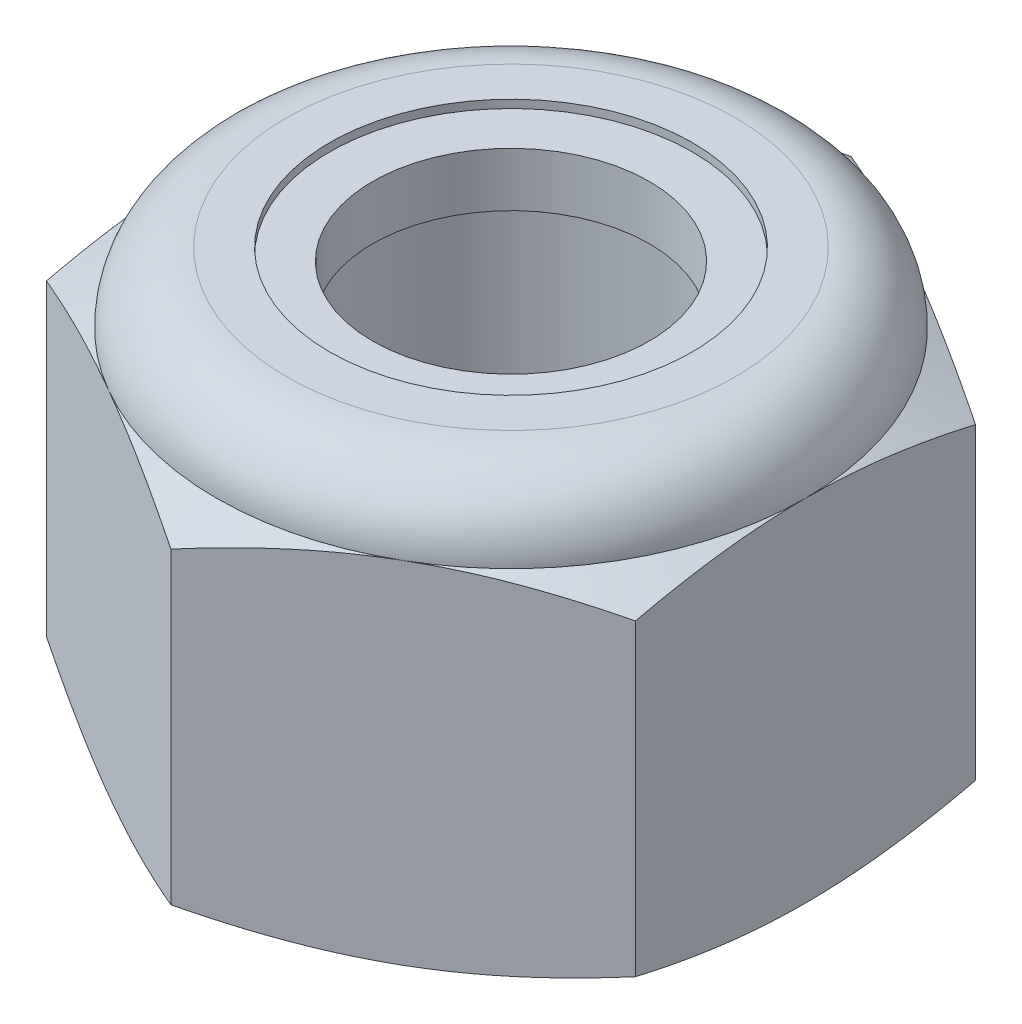
SolidWorks part; units mm, degrees
ref_plane "Front" through (0, 0, 0) normal (0, 0, 1) x (1, 0, 0)
ref_plane "Top" through (0, 0, 0) normal (0, 1, 0) x (1, 0, 0)
ref_plane "Right" through (0, 0, 0) normal (1, 0, 0) x (0, 0, -1)
sketch "Sketch1" plane through (0, 0, 0) normal (0, 1, 0) x (1, 0, 0)
  line L1 (0, 6.4158) -> (-5.5563, 3.2079)
  line L2 (-5.5563, 3.2079) -> (-5.5563, -3.2079)
  line L3 (-5.5563, -3.2079) -> (0, -6.4158)
  line L4 (0, -6.4158) -> (5.5562, -3.2079)
  line L5 (5.5562, -3.2079) -> (5.5562, 3.2079)
  line L6 (5.5562, 3.2079) -> (0, 6.4158)
  circle A0 centre (0, 0) radius 5.5563 construction
  dimension "Hex Flats" = 11.1125
extrude "Extrude1" add sketch "Sketch1" along normal blind 7.9375
sketch "Sketch2" plane through (0, 0, 0) normal (1, 0, 0) x (0, 0, -1)
  line L0 (-3.175, 0) -> (-3.175, 7.9375) construction
  line L1 (0, 0) -> (3.175, 0)
  line L2 (0, 0) -> (0, 7.9375)
  line L3 (0, 7.9375) -> (3.175, 7.9375)
  line L4 (3.175, 0) -> (3.175, 7.9375)
  line L5 (-3.2079, 7.9375) -> (3.2079, 7.9375) construction
  line L7 (0, -3.175) -> (0, 0) construction
  dimension "Thread Dia" = 6.35
revolve "Revolve1" add sketch "Sketch2" angle 360 about L7
sketch "Sketch3" plane through (0, 0, 0) normal (1, 0, 0) x (0, 0, -1)
  line L0 (3.175, 7.9375) -> (-3.175, 7.9375) construction
  line L1 (-3.175, 7.9375) -> (-3.175, 6.6675) construction
  line L2 (-3.175, 6.6675) -> (3.175, 7.9375) construction
  line L3 (3.175, 7.9375) -> (3.2061, 7.7818) construction
  line L4 (3.2061, 7.7818) -> (3.4241, 6.6922)
  line L5 (3.4241, 6.6922) -> (2.6722, 6.9465)
  line L6 (2.6722, 6.9465) -> (2.6099, 7.2579)
  line L7 (2.6099, 7.2579) -> (3.2061, 7.7818)
  line L8 (2.641, 7.1022) -> (3.3151, 7.237) construction
  line L9 (3.175, 7.9375) -> (3.175, 7.209) construction
  line L10 (3.175, 7.209) -> (-3.175, 5.939) construction
  line L11 (-3.175, 5.939) -> (-3.175, 6.6675) construction
  line L12 (-0.2727, 7.9375) -> (0.2727, 5.2105) construction
  line L13 (-3.175, 0) -> (-3.175, 7.9375) construction
  line L14 (0, 7.9375) -> (3.175, 7.9375) construction
  line L15 (3.175, 0) -> (3.175, 7.9375) construction
  point P13 (0, 6.574)
  dimension "D1" = 0.1588
  dimension "D2" = 0.3175
  dimension "Thread Pitch" = 1.27
  dimension "D4" = 60
  dimension "D5" = 1.27
revolve "Cut-Revolve1" [suppressed] cut sketch "Sketch3" angle 360 about L12
pattern_linear "LPattern1" [suppressed] count 6 spacing 1.27 along (0, 1, 0) count 2 spacing 1.27 along (0, 1, 0)
sketch "Sketch4" plane through (0, 0, 0) normal (1, 0, 0) x (0, 0, -1)
  line L0 (0, 7.9375) -> (3.175, 7.9375)
  line L1 (3.175, 7.9375) -> (2.6099, 7.674)
  line L2 (2.6099, 7.674) -> (2.6099, 0.2635)
  line L3 (2.6099, 0.2635) -> (3.175, 0)
  line L4 (3.175, 0) -> (0, 0)
  line L5 (0, 0) -> (0, 7.9375)
  line L6 (3.175, 0) -> (3.175, 7.9375) construction
  line L7 (0, 7.9375) -> (3.175, 7.9375) construction
  line L8 (0, 0) -> (3.175, 0) construction
  line L9 (0, 0) -> (0, 7.9375) construction
  line L10 (0, 7.9375) -> (0, 8.561) construction
  dimension "D1" = 25
revolve "Cut-Revolve2" [suppressed] cut sketch "Sketch4" angle 360 about L10
combine bodies "Combine1" operation type subtract main body 108 bodies to subtract 109
sketch "Sketch5" plane through (0, 0, 0) normal (1, 0, 0) x (0, 0, -1)
  line L0 (0, 0) -> (5.5563, 0)
  line L1 (5.5563, 0) -> (6.4158, 0.4008)
  line L2 (6.4158, 0.4008) -> (6.4158, 6.2138)
  line L3 (6.4158, 6.2138) -> (5.5563, 6.6146)
  line L4 (4.2333, 7.9375) -> (4.2333, 9.2075)
  line L5 (4.2333, 9.2075) -> (7.6858, 9.2075)
  line L6 (7.6858, 9.2075) -> (7.6858, -1.27)
  line L7 (7.6858, -1.27) -> (0, -1.27)
  line L8 (0, -1.27) -> (0, 0)
  line L9 (5.5563, 6.6146) -> (5.5563, 0) construction
  line L10 (0, 0) -> (3.175, 0) construction
  line L13 (6.4158, 3.3073) -> (7.6858, 3.3073) construction
  line L14 (6.4158, 7.9375) -> (6.4158, 0) construction
  line L15 (0, 0) -> (0, 9.2075) construction
  line L20 (0, 9.2075) -> (4.2333, 9.2075) construction
  line L22 (0, 7.9375) -> (3.175, 7.9375) construction
  arc A0 (5.5563, 6.6146) -> (4.2333, 7.9375) centre (4.2333, 6.6146) ccw
  dimension "D1" = 25
  dimension "D2" = 1.27
  dimension "D3" = 7.9375
  dimension "D4" = 1.3229
revolve "Cut-Revolve3" cut sketch "Sketch5" angle 360 about L15
sketch "Sketch6" plane through (0, 0, 0) normal (1, 0, 0) x (0, 0, -1)
  line L0 (0, 6.6146) -> (5.4039, 6.6146)
  line L1 (4.2333, 7.7851) -> (3.4216, 7.7851)
  line L2 (0, 9.2075) -> (0, 6.6146)
  line L3 (3.4216, 9.2075) -> (0, 9.2075)
  line L4 (0, 9.2075) -> (4.2333, 9.2075) construction
  line L5 (0, 0) -> (0, 9.2075) construction
  line L6 (0, 9.2075) -> (0, 44.323) construction
  line L7 (3.4216, 7.7851) -> (3.4216, 9.2075)
  line L8 (4.2333, 7.9375) -> (4.2333, 7.7851) construction
  line L9 (3.4216, 7.7851) -> (2.6099, 7.7851) construction
  line L10 (2.6099, 7.7851) -> (2.6099, 7.674) construction
  arc A0 (5.4039, 6.6146) -> (4.2333, 7.7851) centre (4.2333, 6.6146) ccw
  arc A1 (5.5563, 6.6146) -> (4.2333, 7.9375) centre (4.2333, 6.6146) ccw construction
  dimension "D1" = 0.1524
revolve "Cut-Revolve4" cut sketch "Sketch6" angle 360 about L6
sketch "Sketch7" plane through (0, 0, 0) normal (1, 0, 0) x (0, 0, -1)
  line L0 (2.6099, 6.6908) -> (5.325, 6.6908)
  line L1 (4.2333, 7.7089) -> (2.6099, 7.7089)
  line L2 (2.6099, 7.7089) -> (2.6099, 6.6908)
  line L3 (2.6099, 6.6908) -> (0, 6.6908) construction
  line L4 (0, 6.6908) -> (0, 7.7089) construction
  line L5 (0, 7.7089) -> (2.6099, 7.7089) construction
  line L6 (2.6099, 6.6908) -> (2.6099, 6.6146) construction
  line L7 (0, 6.6146) -> (5.4039, 6.6146) construction
  line L8 (4.2333, 7.7089) -> (4.2333, 7.7851) construction
  arc A0 (5.325, 6.6908) -> (4.2333, 7.7089) centre (4.2333, 6.6146) ccw
  arc A2 (5.4039, 6.6146) -> (4.2333, 7.7851) centre (4.2333, 6.6146) ccw construction
  dimension "D1" = 0.0762
revolve "Revolve2" add sketch "Sketch7" angle 360 about L4
equation "\"D1@Sketch3\"=\"Thread Pitch@Sketch3\"/8"
equation "\"D2@Sketch3\"=\"Thread Pitch@Sketch3\"/4"
equation "\"D5@Sketch3\"=\"Thread Pitch@Sketch3\""
equation "\"D4@LPattern1\"=\"Thread Pitch@Sketch3\""
equation "\"D3@LPattern1\"=\"Thread Pitch@Sketch3\""
equation "\"D1@LPattern1\"=\"Height@Extrude1\"/\"Thread Pitch@Sketch3\""
equation "\"D4@Sketch5\"=\"Height@Extrude1\"/6"
